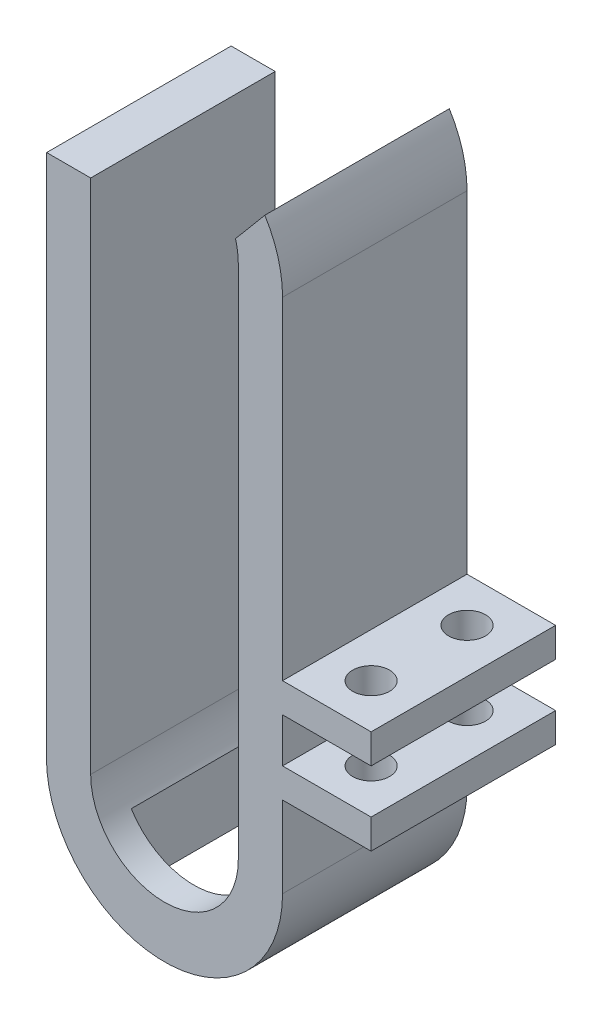
SolidWorks part; units mm, degrees
ref_plane "Front Plane" through (0, 0, 0) normal (0, 0, 1) x (1, 0, 0)
ref_plane "Top Plane" through (0, 0, 0) normal (0, 1, 0) x (1, 0, 0)
ref_plane "Right Plane" through (0, 0, 0) normal (1, 0, 0) x (0, 0, -1)
sketch "Sketch1" plane through (0, 0, 0) normal (0, 0, 1) x (1, 0, 0)
  line L0 (0, 17.5) -> (0, -17.5) construction
  line L1 (5, 17.5) -> (5, -17.5)
  line L2 (-5, 8.5) -> (-5, -17.5)
  line L3 (8, 17) -> (8, -18)
  line L4 (-8, 11.5) -> (-8, -18)
  line L6 (-8, 11.5) -> (-5, 8.5)
  line L9 (-5, 17.5) -> (-5, 8.5)
  line L10 (-8, 17) -> (-8, 11.5)
  line L11 (-6.105, 27.1604) -> (2.0351, 15.5351)
  line L12 (-5, 8.5) -> (2.0351, 15.5351)
  line L13 (-7.9844, 17.5) -> (7.9844, 17.5)
  line L14 (2.0351, 15.5351) -> (9.5686, 24.5132)
  arc A0 (5, 17.5) -> (-5, 17.5) centre (0, 17.5) ccw
  arc A1 (-5, -17.5) -> (5, -17.5) centre (0, -17.5) ccw
  arc A2 (-8, -18) -> (8, -18) centre (0, -18) ccw
  arc A3 (8, 17) -> (-8, 17) centre (0, 17) ccw
  point P2 (0, 0)
  dimension "D4" = 35
  dimension "D7" = 100
  dimension "D8" = 75
  dimension "D1" = 3
  dimension "D2" = 3
  dimension "D3" = 5
  dimension "D5" = 35
  dimension "D6" = 17
extrude "Boss-Extrude1" add sketch "Sketch1" along normal blind 12.5
sketch "Sketch2" plane through (8, 0, 0) normal (1, 0, 0) x (0, 0, -1)
  line L0 (0, 17) -> (0, -18) construction
  line L7 (-12.5, 17) -> (0, 17) construction
  line L8 (-12.5, 17) -> (-12.5, -18) construction
  line L9 (-12.5, -12.5) -> (0, -12.5)
  line L10 (-12.5, -12.5) -> (-12.5, -10.5)
  line L11 (-12.5, -10.5) -> (0, -10.5)
  line L12 (0, -12.5) -> (0, -10.5)
  line L13 (-12.5, -5.5) -> (0, -5.5)
  line L14 (-12.5, -5.5) -> (-12.5, -7.5)
  line L15 (-12.5, -7.5) -> (0, -7.5)
  line L16 (0, -5.5) -> (0, -7.5)
  dimension "D1" = 22.5
  dimension "D2" = 3
  dimension "D3" = 2
  dimension "D4" = 2
extrude "Boss-Extrude2" add sketch "Sketch2" along normal blind 6
sketch "Sketch3" plane through (0, -10.5, 0) normal (0, 1, 0) x (1, 0, 0)
  line L0 (14, 0) -> (8, 0) construction
  line L1 (8, -6.25) -> (14, -6.25) construction
  line L2 (8, 0) -> (8, -12.5) construction
  line L3 (14, 0) -> (14, -12.5) construction
  circle A1 centre (11, -3) radius 1.25
  circle A2 centre (11, -9.5) radius 1.25
  point P10 (11, -9.5)
  dimension "D1" = 3
  dimension "D2" = 2.5
  dimension "D3" = 3
extrude "Cut-Extrude1" cut sketch "Sketch3" against normal through all both and the other way through all
sketch "Sketch5" plane through (0, 0, 0) normal (0, 1, 0) x (1, 0, 0)
  line L1 (-4.25, -2) -> (4.25, -2)
  line L2 (-4.25, -2) -> (-4.25, -10.5)
  line L3 (-4.25, -10.5) -> (4.25, -10.5)
  line L4 (4.25, -2) -> (4.25, -10.5)
  line L5 (-5, -12.5) -> (5, -12.5) construction
  line L6 (-5, -12.5) -> (-5, 0) construction
  point P8 (0, -12.5)
  point P9 (0, -10.5)
  point P12 (-5, -6.25)
  point P13 (-4.25, -6.25)
  dimension "D1" = 8.5
  dimension "D2" = 8.5
extrude "Cut-Extrude2" cut sketch "Sketch5" against normal through all
